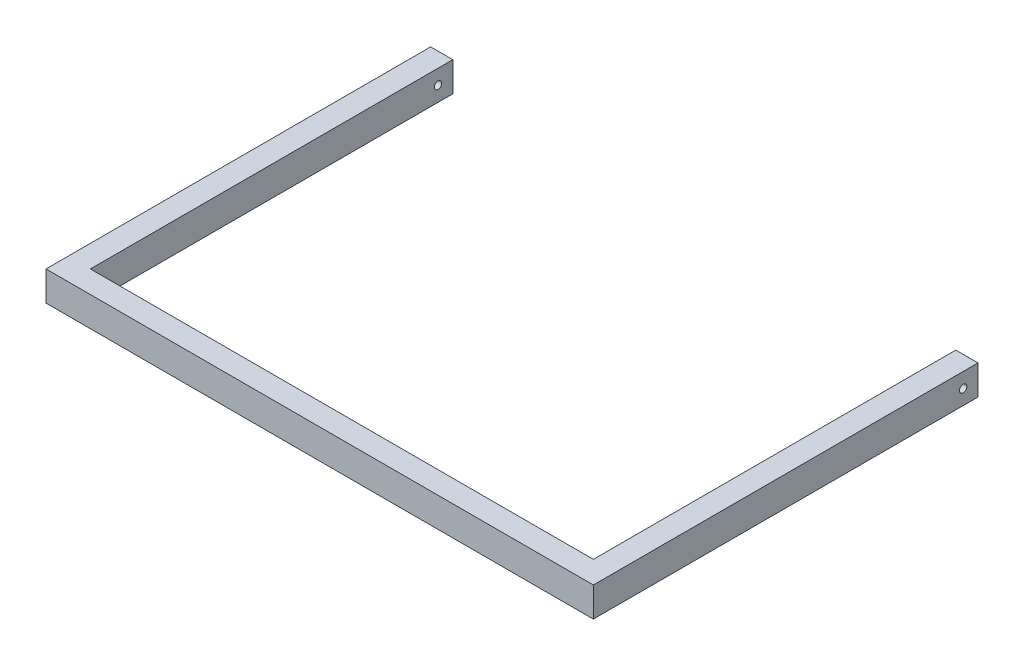
SolidWorks part; units mm, degrees
ref_plane "Спереди" through (0, 0, 0) normal (0, 0, 1) x (1, 0, 0)
ref_plane "Сверху" through (0, 0, 0) normal (0, 1, 0) x (1, 0, 0)
ref_plane "Справа" through (0, 0, 0) normal (1, 0, 0) x (0, 0, -1)
sketch "Эскиз1" plane through (0, 0, 0) normal (0, 1, 0) x (1, 0, 0)
  line L0 (1.5324, 486.843) -> (1.5324, -3.157)
  line L1 (1.5324, -3.157) -> (681.5324, -3.157)
  line L2 (681.5324, -3.157) -> (681.5324, 486.843)
  line L3 (-28.4676, 486.843) -> (1.5324, 486.843)
  line L4 (-28.4676, 486.843) -> (-28.4676, -33.157)
  line L5 (-28.4676, -33.157) -> (711.5324, -33.157)
  line L6 (711.5324, -33.157) -> (711.5324, 486.843)
  line L7 (711.5324, 486.843) -> (681.5324, 486.843)
  line L8 (-250.4728, 486.843) -> (1027.9214, 486.843) construction
  dimension "D1" = 30
  dimension "D2" = 30
  dimension "D3" = 520
  dimension "D4" = 30
  dimension "D5" = 680
extrude "Бобышка-Вытянуть1" add sketch "Эскиз1" along normal blind 40
sketch "Эскиз2" plane through (711.5324, 0, 0) normal (1, 0, 0) x (0, 0, -1)
  line L0 (466.843, 40) -> (466.843, 0) construction
  line L1 (-33.157, 40) -> (486.843, 40) construction
  line L2 (-33.157, 0) -> (486.843, 0) construction
  line L3 (486.843, 40) -> (486.843, 0) construction
  circle A0 centre (466.843, 20) radius 5
  dimension "D1" = 10
  dimension "D2" = 20
extrude "Вырез-Вытянуть1" cut sketch "Эскиз2" against normal through all
chamfer "Фаска1" [suppressed] distance 20 angle 52
chamfer "Фаска2" [suppressed] distance 25 angle 16
